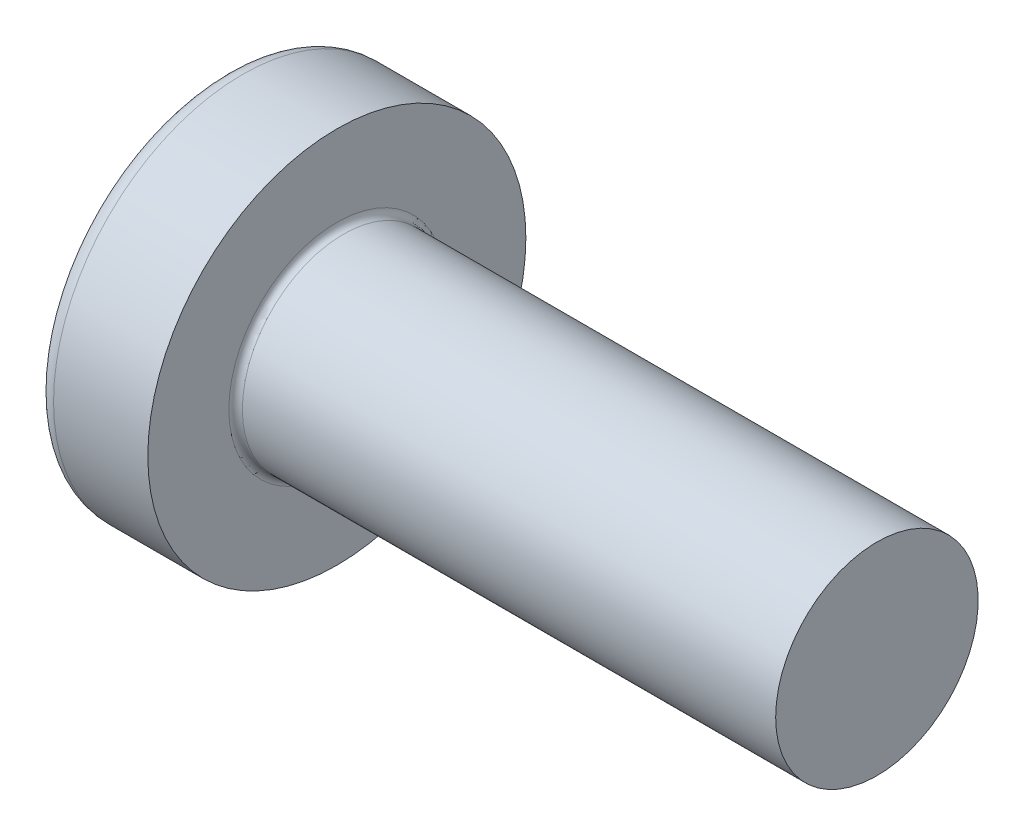
SolidWorks part; units mm, degrees
material "Alliage 7079"
ref_plane "Plane1" through (0, 0, 0) normal (0, 0, 1) x (1, 0, 0)
ref_plane "Plane2" through (0, 0, 0) normal (0, 1, 0) x (1, 0, 0)
ref_plane "Plane3" through (0, 0, 0) normal (1, 0, 0) x (0, 0, -1)
sketch "BodySke" plane through (0, 0, 0) normal (0, 0, 1) x (1, 0, 0)
  line L0 (2.4, 1.5) -> (2.4, 2.8)
  line L1 (2.65, 6.35) -> (2.65, -3.175) construction
  line L2 (-25.4, 0) -> (127, 0) construction
  line L3 (10.4, 0) -> (0, 0)
  line L4 (2.4, 1.5) -> (10.4, 1.5)
  line L5 (10.4, 1.5) -> (10.4, 0)
  line L6 (1.0035, 2.8) -> (2.4, 2.8)
  line L8 (2.4, 6.35) -> (2.4, -3.175) construction
  arc A0 (0.7754, 2.6744) -> (0, 0) centre (5, 0) ccw
  arc A2 (0.7754, 2.6744) -> (1.0035, 2.8) centre (1.0035, 2.53) cw
  dimension "Head_fillet_rad" = 0.27
  dimension "Head_crown_rad" = 5
  dimension "Head_ht" = 2.4
  dimension "Diameter" = 3
  dimension "Length" = 8
  dimension "Head_dia" = 5.6
  dimension "Advance" = 0.5
  dimension "Thread_nom" = 8
revolve "Base-Revolve" add sketch "BodySke"
cosmetic thread "ThreadCosmetic"
fillet "Fillet1" radius 0.1 1 edges at (2.4, 0, 1.5)
sketch "Sketch3" plane through (0, 0, 0) normal (1, 0, 0) x (0, 0, -1)
  line L0 (0.37, -1.4) -> (-0.37, -1.4)
  line L1 (0.37, -1.4) -> (0.37, 1.4)
  line L2 (-0.37, 1.4) -> (0.37, 1.4)
  line L3 (-0.37, 1.4) -> (-0.37, -1.4)
  dimension "D1" = 1.4
  dimension "Cross_dia" = 2.8
  dimension "D2" = 0.37
  dimension "Cross_width" = 0.74
ref_plane "Plane4" through (1.75, 0, 0) normal (1, 0, 0) x (0, 0, -1)
sketch "Sketch4" plane through (1.75, 0, 0) normal (1, 0, 0) x (0, 0, -1)
  line L0 (0.37, -0.5275) -> (-0.37, -0.5275)
  line L1 (0.37, -0.5275) -> (0.37, 0.5275)
  line L2 (-0.37, 0.5275) -> (0.37, 0.5275)
  line L3 (-0.37, 0.5275) -> (-0.37, -0.5275)
  dimension "D1" = 0.74
  dimension "D2" = 1.055
  dimension "D3" = 0.37
  dimension "D4" = 0.5275
loft "Recess" cut profiles "Sketch3", "Sketch4"
pattern_circular "RecPat" count 2 every 90 about axis through (0, 0, 0) along (1, 0, 0) of "Recess"
sketch "RecCorSke" plane through (0, 0, 0) normal (0, 0, 1) x (1, 0, 0)
  line L0 (-3.175, 0) -> (15.875, 0) construction
  line L1 (-25.4, 0) -> (127, 0) construction
  line L2 (0, 0) -> (0, 0.6784)
  line L3 (0, 0.6784) -> (1.75, 0.556)
  line L4 (1.75, 0.556) -> (1.9307, 0)
  line L5 (1.9307, 0) -> (0, 0)
  dimension "Diameter" = 1.112
  dimension "Depth" = 1.75
  dimension "Draft_angle" = 4
  dimension "Bottom_angle" = 18
revolve "RecessCore" cut sketch "RecCorSke" angle 360 about L0
sketch "ThdSchSke" plane through (0, 0, 0) normal (0, 0, 1) x (1, 0, 0)
  line L0 (3.4, -1.2195) -> (3.2036, -1.5)
  line L1 (3.4, -1.2195) -> (3.5964, -1.5)
  line L2 (3.5964, -1.5) -> (3.5964, -1.875)
  line L3 (-3.175, 0) -> (5.1513, 0) construction
  line L5 (3.5964, -1.875) -> (3.2036, -1.875)
  line L6 (3.2036, -1.875) -> (3.2036, -1.5)
  dimension "Thread_minor" = 2.439
  dimension "Diameter" = 3
  dimension "Start" = 3.4
  dimension "SideAngle" = 55
  dimension "VeeAngle" = 70
  dimension "Overcut" = 3.75
revolve "ThreadSchematic" [suppressed] cut sketch "ThdSchSke" angle 360 about L3
pattern_linear "ThdSchPat" [suppressed]
equation "\"D1@Sketch3\" = \"Cross_dia@Sketch3\" / 2"
equation "\"D2@Sketch3\" = \"Cross_width@Sketch3\" / 2"
equation "\"Depth@RecCorSke\" = \"Cross_depth@Plane4\""
equation "\"D1@Sketch4\" = \"Cross_width@Sketch3\""
equation "\"D2@Sketch4\" = \"Cross_dia@Sketch3\" - 2.0 * \"Cross_depth@Plane4\" * tan(26.5  * 0.017453292)"
equation "\"D3@Sketch4\" = \"D1@Sketch4\" / 2"
equation "\"D4@Sketch4\" = \"D2@Sketch4\" / 2"
equation "\"Thread_length@ThreadCosmetic\" = ((sgn( (\"Length@BodySke\" - \"Advance@BodySke\" * 2.0 ) - \"Thread_nom@BodySke\" )-1)*( (\"Length@BodySke\" - \"Advance@BodySke\" * 2.0 ) - \"Thread_nom@BodySke\" ))/-2+ \"Thread_nom@BodySke\""
equation "\"Thread_minor@ThdSchSke\" = \"Thread_minor@ThreadCosmetic\""
equation "\"Diameter@ThdSchSke\" = \"Diameter@BodySke\""
equation "\"Overcut@ThdSchSke\" = \"Diameter@BodySke\" * 1.25"
equation "\"Start@ThdSchSke\" = \"Head_ht@BodySke\" + \"Length@BodySke\" - \"Thread_length@ThreadCosmetic\"  '---Non-countersunk---"
equation "\"Num_threads@ThdSchPat\" = int( \"Thread_length@ThreadCosmetic\" / \"Advance@BodySke\" + 0.999 )  + 1"
equation "\"Advance@ThdSchPat\" = \"Thread_length@ThreadCosmetic\" /  (\"Num_threads@ThdSchPat\" - 1) 'relax it"
